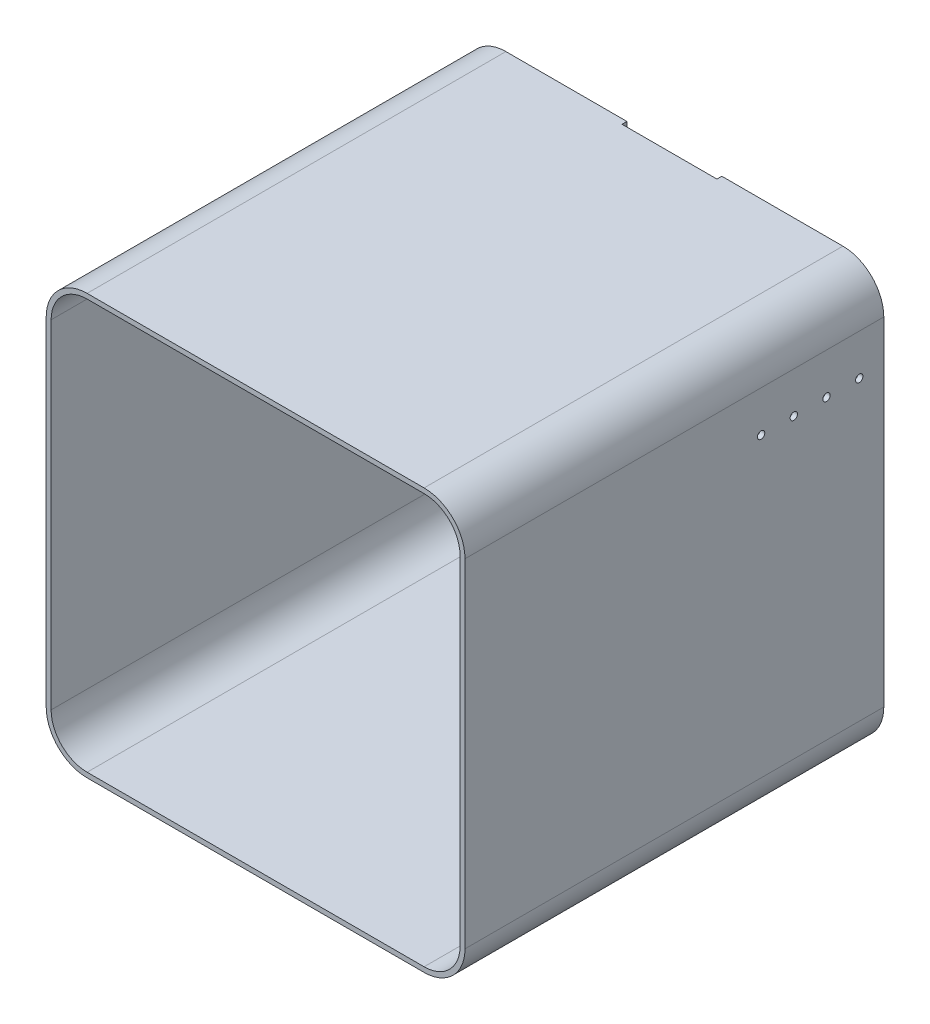
SolidWorks part; units mm, degrees
material "Pine"
ref_plane "Front Plane" through (0, 0, 0) normal (0, 0, 1) x (1, 0, 0)
ref_plane "Top Plane" through (0, 0, 0) normal (0, 1, 0) x (1, 0, 0)
ref_plane "Right Plane" through (0, 0, 0) normal (1, 0, 0) x (0, 0, -1)
sketch "Sketch1" plane through (0, 0, 0) normal (0, 0, 1) x (1, 0, 0)
  line L1 (44, 0) -> (456, 0)
  line L2 (0, 44) -> (0, 457)
  line L3 (44, 501) -> (456, 501)
  line L4 (500, 44) -> (500, 457)
  arc A0 (0, 457) -> (44, 501) centre (44, 457) cw
  arc A1 (456, 501) -> (500, 457) centre (456, 457) cw
  arc A2 (456, 0) -> (500, 44) centre (456, 44) ccw
  arc A3 (44, 0) -> (0, 44) centre (44, 44) cw
  point P9 (0, 501)
  point P12 (500, 501)
  point P15 (500, 0)
  point P18 (0, 0)
  dimension "D3" = 44
  dimension "D4" = 44
  dimension "D5" = 44
  dimension "D6" = 44
  dimension "D1" = 500
  dimension "D2" = 501
extrude "Extrude-Thin1" add sketch "Sketch1" against normal blind 512 thin contours A0 L3 A1 L4 A2 L1 A3 L2
sketch "Sketch3" plane through (506, 0, 0) normal (1, 0, 0) x (0, 0, -1)
  line L0 (512, 44) -> (512, 457) construction
  line L1 (512, 457) -> (0, 457) construction
  circle A0 centre (482, 407) radius 4.5
  dimension "D1" = 30
  dimension "D2" = 9
  dimension "D3" = 50
extrude "Cut-Extrude1" cut sketch "Sketch3" against normal blind 10
pattern_linear "LPattern1" count 4 spacing 40 along (0, 0, 1) of "Cut-Extrude1"
sketch "Sketch4" plane through (0, 0, -512) normal (0, 0, -1) x (-1, 0, 0)
  line L0 (-44, 507) -> (-456, 507) construction
  line L1 (-44, 501) -> (-456, 501) construction
  line L2 (-308, 507) -> (-192, 507)
  line L3 (-308, 507) -> (-308, 501)
  line L4 (-308, 501) -> (-192, 501)
  line L5 (-192, 507) -> (-192, 501)
  dimension "D1" = 6
  dimension "D2" = 148
  dimension "D3" = 148
extrude "Cut-Extrude2" cut sketch "Sketch4" against normal blind 6
